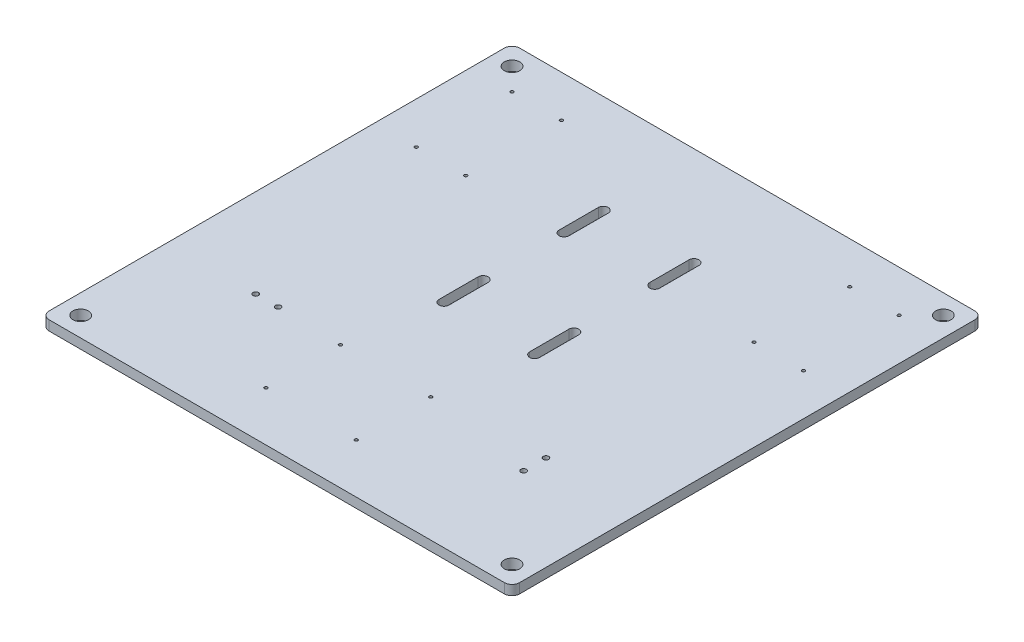
SolidWorks part; units mm, degrees
ref_plane "Front Plane" through (0, 0, 0) normal (0, 0, 1) x (1, 0, 0)
ref_plane "Top Plane" through (0, 0, 0) normal (0, 1, 0) x (1, 0, 0)
ref_plane "Right Plane" through (0, 0, 0) normal (1, 0, 0) x (0, 0, -1)
sketch "Sketch2" plane through (0, 0, 0) normal (0, 1, 0) x (1, 0, 0)
  line L0 (24.0083, -83.3289) -> (24.0083, 221.4711) construction
  line L1 (-128.3917, -83.3289) -> (176.4083, -83.3289)
  line L2 (-128.3917, -83.3289) -> (-128.3917, 221.4711)
  line L3 (-128.3917, 221.4711) -> (176.4083, 221.4711)
  line L4 (176.4083, -83.3289) -> (176.4083, 221.4711)
  line L5 (-103.3917, 196.4711) -> (-67.3917, 196.4711)
  line L6 (-103.3917, 196.4711) -> (-103.3917, 130.4711)
  line L7 (-103.3917, 130.4711) -> (-67.3917, 130.4711)
  line L8 (-67.3917, 196.4711) -> (-67.3917, 130.4711)
  line L9 (-128.3917, 69.0711) -> (176.4083, 69.0711) construction
  line L10 (151.4083, 130.4711) -> (115.4083, 130.4711)
  line L11 (115.4083, 196.4711) -> (115.4083, 130.4711)
  line L12 (151.4083, 196.4711) -> (115.4083, 196.4711)
  line L13 (151.4083, 196.4711) -> (151.4083, 130.4711)
  line L15 (-73.6917, 0.8711) -> (-53.6917, 0.8711)
  line L16 (-73.6917, 0.8711) -> (-73.6917, -15.1289)
  line L17 (-73.6917, -15.1289) -> (-53.6917, -15.1289)
  line L18 (-53.6917, 0.8711) -> (-53.6917, -15.1289)
  line L22 (-85.3917, 130.4711) -> (-85.3917, 196.4711) construction
  line L27 (24.0083, -83.3289) -> (24.0083, -41.2289) construction
  line L28 (24.0083, -9.4789) -> (24.0083, 105.9711) construction
  line L29 (-103.3917, 163.4711) -> (-67.3917, 163.4711) construction
  line L30 (133.4083, 196.4711) -> (133.4083, 130.4711) construction
  line L31 (115.4083, 163.4711) -> (151.4083, 163.4711) construction
  line L32 (113.2083, 1.8711) -> (116.2356, 1.8711) construction
  line L34 (-63.6917, 0.8711) -> (-63.6917, -15.1289) construction
  line L35 (-73.6917, -7.1289) -> (-53.6917, -7.1289) construction
  line L40 (-18.7907, -27.1949) -> (66.8073, -27.1949) construction
  line L43 (1.0083, 28.9711) -> (47.0083, 28.9711)
  line L44 (1.0083, 28.9711) -> (1.0083, 182.9711)
  line L45 (1.0083, 182.9711) -> (47.0083, 182.9711)
  line L46 (47.0083, 28.9711) -> (47.0083, 182.9711)
  line L47 (1.0083, 28.9711) -> (47.0083, 182.9711) construction
  line L48 (1.0083, 182.9711) -> (47.0083, 28.9711) construction
  line L56 (-102.3917, 131.4711) -> (-102.3917, 133.6768) construction
  line L57 (-103.3917, 130.4711) -> (-102.3917, 130.4711)
  line L58 (-103.3917, 130.4711) -> (-103.3917, 131.4711)
  line L59 (-103.3917, 131.4711) -> (-102.3917, 131.4711)
  line L60 (-102.3917, 130.4711) -> (-102.3917, 131.4711)
  line L61 (-102.3917, 131.4711) -> (-100.139, 131.4711) construction
  line L62 (-67.3917, 131.4711) -> (-68.3917, 131.4711)
  line L63 (-68.3917, 130.4711) -> (-68.3917, 131.4711)
  line L64 (-67.3917, 130.4711) -> (-68.3917, 130.4711)
  line L65 (-67.3917, 130.4711) -> (-67.3917, 131.4711)
  line L66 (-68.3917, 131.4711) -> (-70.6443, 131.4711) construction
  line L67 (-68.3917, 131.4711) -> (-68.3917, 133.6768) construction
  line L68 (-102.3917, 195.4711) -> (-102.3917, 193.2654) construction
  line L69 (-102.3917, 195.4711) -> (-100.139, 195.4711) construction
  line L70 (-103.3917, 195.4711) -> (-102.3917, 195.4711)
  line L71 (-102.3917, 196.4711) -> (-102.3917, 195.4711)
  line L72 (-103.3917, 196.4711) -> (-102.3917, 196.4711)
  line L73 (-103.3917, 196.4711) -> (-103.3917, 195.4711)
  line L74 (-67.3917, 196.4711) -> (-68.3917, 196.4711)
  line L75 (-68.3917, 196.4711) -> (-68.3917, 195.4711)
  line L76 (-67.3917, 195.4711) -> (-68.3917, 195.4711)
  line L77 (-67.3917, 196.4711) -> (-67.3917, 195.4711)
  line L78 (-68.3917, 195.4711) -> (-70.6443, 195.4711) construction
  line L79 (-68.3917, 195.4711) -> (-68.3917, 193.2654) construction
  line L81 (111.7083, -17.6289) -> (134.7083, -17.6289)
  line L82 (111.7083, -17.6289) -> (111.7083, 3.3711)
  line L83 (111.7083, 3.3711) -> (134.7083, 3.3711)
  line L84 (134.7083, -17.6289) -> (134.7083, 3.3711)
  line L85 (111.7083, -17.6289) -> (134.7083, 3.3711) construction
  line L86 (111.7083, 3.3711) -> (134.7083, -17.6289) construction
  line L89 (111.7083, 3.3711) -> (113.2083, 3.3711)
  line L90 (111.7083, 3.3711) -> (111.7083, 1.8711)
  line L91 (111.7083, 1.8711) -> (113.2083, 1.8711)
  line L92 (113.2083, 3.3711) -> (113.2083, 1.8711)
  line L93 (113.2083, 1.8711) -> (113.2083, 0) construction
  line L94 (111.7083, -7.1289) -> (134.7083, -7.1289) construction
  line L95 (-72.6917, -0.2465) -> (-70.7311, -0.2465) construction
  line L96 (-73.6917, 0.8711) -> (-72.6917, 0.8711)
  line L97 (-73.6917, 0.8711) -> (-73.6917, -0.2465)
  line L98 (-73.6917, -0.2465) -> (-72.6917, -0.2465)
  line L99 (-72.6917, 0.8711) -> (-72.6917, -0.2465)
  line L100 (-72.6917, -0.2465) -> (-72.6917, -1.1609) construction
  line L101 (47.0083, 105.9711) -> (1.0083, 105.9711) construction
  line L103 (56.5833, 54.3711) -> (56.5833, 79.7711)
  line L104 (50.1833, 54.3711) -> (50.1833, 79.7711)
  line L106 (56.5833, 157.5711) -> (56.5833, 132.1711)
  line L107 (50.1833, 157.5711) -> (50.1833, 132.1711)
  line L108 (-8.5667, 157.5711) -> (-8.5667, 132.1711)
  line L109 (-2.1667, 157.5711) -> (-2.1667, 132.1711)
  line L110 (-8.5667, 54.3711) -> (-8.5667, 79.7711)
  line L111 (-2.1667, 54.3711) -> (-2.1667, 79.7711)
  line L112 (-18.7907, -55.1349) -> (66.8073, -55.1349)
  line L113 (176.4083, 221.4711) -> (163.7083, 221.4711)
  line L114 (176.4083, 221.4711) -> (176.4083, 208.7711)
  line L115 (176.4083, 208.7711) -> (163.7083, 208.7711)
  line L116 (163.7083, 221.4711) -> (163.7083, 208.7711)
  line L117 (176.4083, 221.4711) -> (163.7083, 208.7711) construction
  line L118 (176.4083, 208.7711) -> (163.7083, 221.4711) construction
  line L119 (-18.7907, -55.1349) -> (-18.7907, 0.7451)
  line L120 (-18.7907, 0.7451) -> (66.8073, 0.7451)
  line L121 (66.8073, -55.1349) -> (66.8073, 0.7451)
  line L122 (-18.7907, -55.1349) -> (66.8073, 0.7451) construction
  line L123 (-18.7907, 0.7451) -> (66.8073, -55.1349) construction
  line L124 (66.8073, 0.7451) -> (43.4393, 0.7451)
  line L125 (66.8073, 0.7451) -> (66.8073, -55.1349)
  line L126 (66.8073, -55.1349) -> (43.4393, -55.1349)
  line L127 (43.4393, 0.7451) -> (43.4393, -55.1349)
  line L128 (66.8073, 0.7451) -> (43.4393, -55.1349) construction
  line L129 (66.8073, -55.1349) -> (43.4393, 0.7451) construction
  line L130 (-18.7907, 0.7451) -> (-14.9807, 0.7451)
  line L131 (-18.7907, 0.7451) -> (-18.7907, -3.0649)
  line L132 (-18.7907, -3.0649) -> (-14.9807, -3.0649)
  line L133 (-14.9807, 0.7451) -> (-14.9807, -3.0649)
  line L134 (-18.7907, 0.7451) -> (-14.9807, -3.0649) construction
  line L135 (-18.7907, -3.0649) -> (-14.9807, 0.7451) construction
  circle A2 centre (-101.3917, 132.4711) radius 1
  circle A3 centre (-69.3917, 132.4711) radius 1
  circle A4 centre (-101.3917, 194.4711) radius 1
  circle A5 centre (-69.3917, 194.4711) radius 1
  circle A6 centre (149.4083, 132.4711) radius 1
  circle A7 centre (117.4083, 132.4711) radius 1
  circle A8 centre (117.4083, 194.4711) radius 1
  circle A9 centre (149.4083, 194.4711) radius 1
  circle A10 centre (114.9583, 0.1211) radius 1.75
  circle A11 centre (114.9583, -14.3789) radius 1.75
  circle A12 centre (-70.9417, -1.9965) radius 1.75
  circle A13 centre (-56.4417, -1.9965) radius 1.75
  arc A14 (56.5833, 79.7711) -> (50.1833, 79.7711) centre (53.3833, 79.7711) ccw
  arc A16 (56.5833, 54.3711) -> (50.1833, 54.3711) centre (53.3833, 54.3711) cw
  arc A17 (56.5833, 157.5711) -> (50.1833, 157.5711) centre (53.3833, 157.5711) ccw
  arc A18 (56.5833, 132.1711) -> (50.1833, 132.1711) centre (53.3833, 132.1711) cw
  arc A19 (-8.5667, 132.1711) -> (-2.1667, 132.1711) centre (-5.3667, 132.1711) ccw
  arc A20 (-8.5667, 157.5711) -> (-2.1667, 157.5711) centre (-5.3667, 157.5711) cw
  arc A21 (-8.5667, 54.3711) -> (-2.1667, 54.3711) centre (-5.3667, 54.3711) ccw
  arc A22 (-8.5667, 79.7711) -> (-2.1667, 79.7711) centre (-5.3667, 79.7711) cw
  circle A23 centre (163.7083, 208.7711) radius 5
  circle A24 centre (-115.6917, 208.7711) radius 5
  circle A25 centre (163.7083, -70.6289) radius 5
  circle A26 centre (-115.6917, -70.6289) radius 5
  circle A27 centre (43.4393, -3.0649) radius 1.016
  circle A28 centre (43.4393, -51.3249) radius 1.016
  circle A29 centre (-14.9807, -3.0649) radius 1.016
  circle A30 centre (-14.9807, -51.3249) radius 1.016
  point P20 (123.2083, -7.1289)
  point P24 (24.0083, 69.0711)
  point P25 (24.0083, -27.1949)
  point P134 (170.0583, 215.1211)
  point P147 (55.1233, -27.1949)
  point P155 (-16.8857, -1.1599)
  dimension "D18" = 23
  dimension "D24" = 1
  dimension "D26" = 2
  dimension "D31" = 12.7
  dimension "D11" = 10
  dimension "D12" = 14.5
  dimension "D13" = 112.3
  dimension "D37" = 2.032
  dimension "D38" = 3.81
  dimension "D41" = 2.032
  dimension "D1" = 304.8
  dimension "D2" = 304.8
  dimension "D3" = 66
  dimension "D4" = 36
  dimension "D5" = 25
  dimension "D6" = 25
  dimension "D7" = 20
  dimension "D8" = 16
  dimension "D9" = 54.7
  dimension "D10" = 68.2
  dimension "D14" = 46
  dimension "D15" = 154
  dimension "D16" = 1
  dimension "D17" = 1
  dimension "D19" = 21
  dimension "D20" = 41.7
  dimension "D21" = 65.7
  dimension "D22" = 1.5
  dimension "D23" = 1.5
  dimension "D25" = 1.1176
  dimension "D27" = 12.7
  dimension "D28" = 3.175
  dimension "D29" = 6.4
  dimension "D30" = 25.4
  dimension "D32" = 85.598
  dimension "D33" = 42.799
  dimension "D34" = 56.134
  dimension "D35" = 55.88
  dimension "D36" = 23.368
  dimension "D39" = 3.81
  dimension "D40" = 3.81
extrude "Boss-Extrude1" add sketch "Sketch2" along normal blind 6.35 contours A12 | A13 | A2 | A3 | A18 L106 A17 L107 | A16 L103 A14 L104 | A20 L108 A19 L109 | A22 L110 A21 L111 | A10 | A11 | L1 L4 L3 L2 | A5 | A4 | A7 | A6 | A9 | A8 | A23 | A24 | A25 | A26 | A30 | A29 | A27 | A28
fillet "Fillet1" radius 5 1 edges at (176.4083, 3.175, -221.4711)
fillet "Fillet2" radius 5 1 edges at (-128.3917, 3.175, -221.4711)
fillet "Fillet3" radius 5 1 edges at (-128.3917, 3.175, 83.3289)
fillet "Fillet4" radius 5 1 edges at (176.4083, 3.175, 83.3289)
